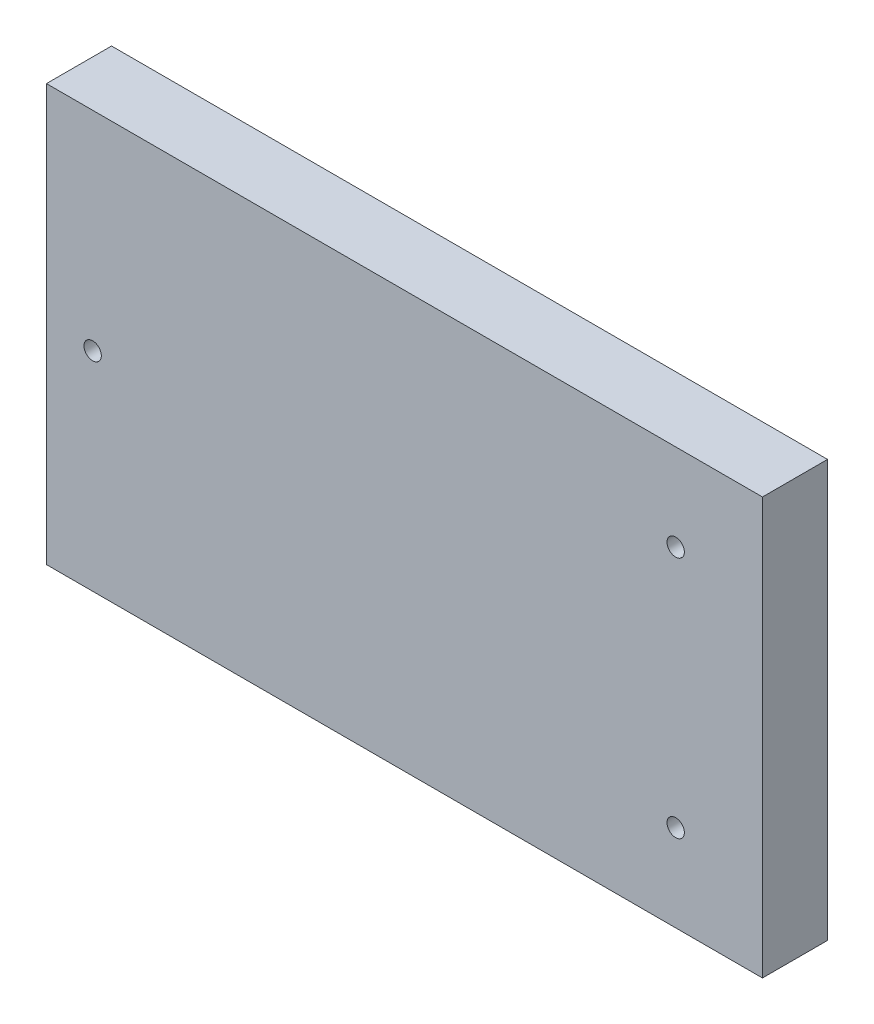
SolidWorks part; units mm, degrees
material "Balsa"
ref_plane "Front Plane" through (0, 0, 0) normal (0, 0, 1) x (1, 0, 0)
ref_plane "Top Plane" through (0, 0, 0) normal (0, 1, 0) x (1, 0, 0)
ref_plane "Right Plane" through (0, 0, 0) normal (1, 0, 0) x (0, 0, -1)
sketch "Sketch1" plane through (0, 0, 0) normal (0, 0, 1) x (1, 0, 0)
  line L0 (525.5345, 316.5094) -> (705.5345, 316.5094) construction
  line L1 (705.5345, 316.5094) -> (540.5345, 316.5094)
  line L2 (705.5345, 316.5094) -> (705.5345, 220.5094)
  line L3 (705.5345, 220.5094) -> (540.5345, 220.5094)
  line L4 (540.5345, 316.5094) -> (540.5345, 220.5094)
  line L5 (705.5345, 220.5094) -> (525.5345, 220.5094) construction
  line L7 (525.5345, 220.5094) -> (525.5345, 316.5094) construction
  circle A0 centre (685.5345, 296.5094) radius 2
  circle A1 centre (685.5345, 240.5094) radius 2
  circle A2 centre (551.1836, 268.5094) radius 2
  dimension "D1" = 165
  dimension "D2" = 15
extrude "Boss-Extrude1" add sketch "Sketch1" along normal blind 15
